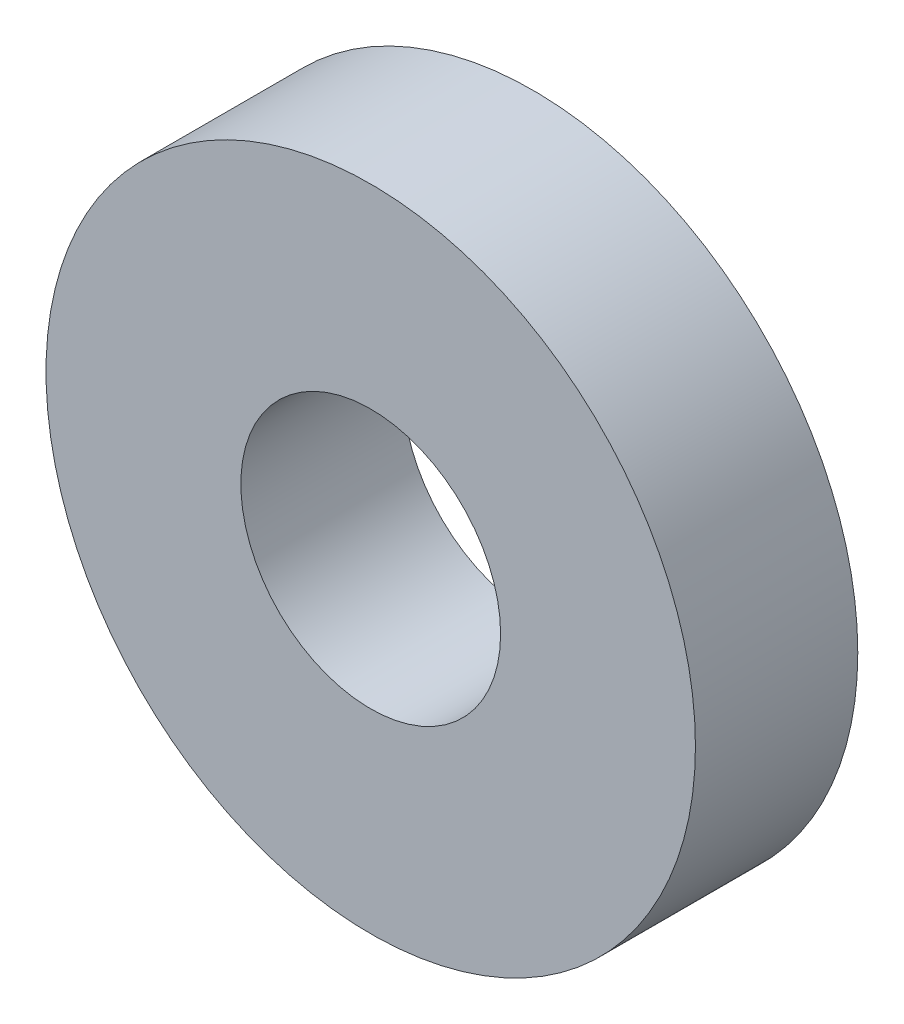
SolidWorks part; units mm, degrees
ref_plane "Front Plane" through (0, 0, 0) normal (0, 0, 1) x (1, 0, 0)
ref_plane "Top Plane" through (0, 0, 0) normal (0, 1, 0) x (1, 0, 0)
ref_plane "Right Plane" through (0, 0, 0) normal (1, 0, 0) x (0, 0, -1)
sketch "Sketch1" plane through (0, 0, 0) normal (0, 0, 1) x (1, 0, 0)
  circle A0 centre (0, 0) radius 4
  circle A1 centre (0, 0) radius 10
  dimension "D1" = 20
  dimension "D2" = 8
extrude "Boss-Extrude1" add sketch "Sketch1" along normal blind 5
